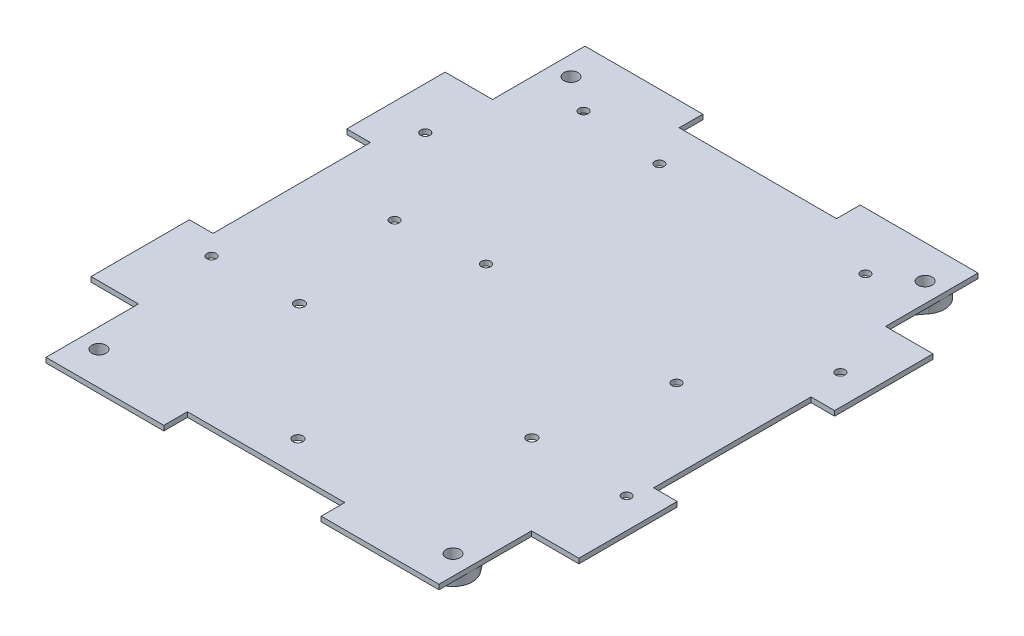
SolidWorks part; units mm, degrees
ref_plane "Front Plane" through (0, 0, 0) normal (0, 0, 1) x (1, 0, 0)
ref_plane "Top Plane" through (0, 0, 0) normal (0, 1, 0) x (1, 0, 0)
ref_plane "Right Plane" through (0, 0, 0) normal (1, 0, 0) x (0, 0, -1)
sketch "Sketch1" plane through (0, 0, 0) normal (0, 1, 0) x (1, 0, 0)
  line L0 (-25.4, 86.995) -> (-63.4314, 86.995)
  line L1 (-88.9, -101.6) -> (88.9, -101.6) construction
  line L2 (101.6, -88.9) -> (101.6, 88.9) construction
  line L3 (88.9, 101.6) -> (-88.9, 101.6) construction
  line L4 (-78.74, -60.96) -> (-63.4314, -60.96)
  line L5 (-63.4314, -60.96) -> (-63.4314, -86.995)
  line L6 (-63.4314, -86.995) -> (-25.4, -86.995)
  line L7 (63.4314, -86.995) -> (63.4314, -60.96)
  line L8 (63.4314, -60.96) -> (78.74, -60.96)
  line L9 (78.74, -60.96) -> (78.74, -25.4)
  line L10 (78.74, 60.96) -> (63.4314, 60.96)
  line L11 (63.4314, 60.96) -> (63.4314, 86.995)
  line L12 (63.4314, 86.995) -> (25.4, 86.995)
  line L13 (-63.4314, 86.995) -> (-63.4314, 60.96)
  line L14 (-63.4314, 60.96) -> (-78.74, 60.96)
  line L15 (-78.74, 60.96) -> (-78.74, 25.4)
  line L16 (-78.74, -25.4) -> (-78.74, -60.96)
  line L17 (-78.74, -25.4) -> (-71.12, -25.4)
  line L19 (-78.74, 25.4) -> (-71.12, 25.4)
  line L20 (-71.12, -25.4) -> (-71.12, 25.4)
  line L22 (-25.4, 86.995) -> (-25.4, 79.375)
  line L23 (-25.4, 79.375) -> (25.4, 79.375)
  line L24 (25.4, 86.995) -> (25.4, 79.375)
  line L25 (78.74, 25.4) -> (71.12, 25.4)
  line L27 (78.74, -25.4) -> (71.12, -25.4)
  line L28 (71.12, 25.4) -> (71.12, -25.4)
  line L30 (25.4, -86.995) -> (25.4, -79.375)
  line L31 (25.4, -79.375) -> (-25.4, -79.375)
  line L32 (-25.4, -86.995) -> (-25.4, -79.375)
  line L33 (78.74, 25.4) -> (78.74, 60.96)
  line L34 (25.4, -86.995) -> (63.4314, -86.995)
  line L35 (-101.6, 88.9) -> (-101.6, -88.9) construction
  line L36 (-78.74, 25.4) -> (-78.74, -25.4)
  line L37 (78.74, 25.4) -> (78.74, -25.4)
  line L38 (-78.74, 0) -> (-91.44, 0)
  line L39 (78.74, 0) -> (91.44, 0)
  line L40 (-91.44, -57.15) -> (-91.44, 57.15)
  line L41 (91.44, -57.15) -> (91.44, 57.15)
  line L42 (-91.44, -57.15) -> (-78.74, -57.15)
  line L43 (-91.44, 57.15) -> (-78.74, 57.15)
  line L44 (91.44, 57.15) -> (78.74, 57.15)
  line L45 (91.44, -57.15) -> (78.74, -57.15)
  line L46 (-78.74, -57.15) -> (-63.4314, -57.15)
  line L47 (-63.4314, -57.15) -> (-63.4314, -60.96)
  line L48 (78.74, -57.15) -> (63.4314, -57.15)
  line L49 (63.4314, -57.15) -> (63.4314, -60.96)
  line L50 (78.74, 57.15) -> (63.4314, 57.15)
  line L51 (63.4314, 57.15) -> (63.4314, 60.96)
  line L52 (-78.74, 57.15) -> (-63.4314, 57.15)
  line L53 (-63.4314, 57.15) -> (-63.4314, 60.96)
  arc A0 (88.9, -101.6) -> (101.6, -88.9) centre (88.9, -88.9) ccw construction
  arc A1 (-101.6, -88.9) -> (-88.9, -101.6) centre (-88.9, -88.9) ccw construction
  arc A2 (101.6, 88.9) -> (88.9, 101.6) centre (88.9, 88.9) ccw construction
  arc A3 (-101.6, 88.9) -> (-88.9, 101.6) centre (-88.9, 88.9) cw construction
  circle A4 centre (-57.15, 76.2) radius 2.286
  circle A5 centre (57.15, 76.2) radius 2.286
  circle A6 centre (57.15, -76.2) radius 2.286
  circle A7 centre (-57.15, -76.2) radius 2.286
  point P3 (0, 101.6)
  point P5 (101.6, 0)
  point P13 (101.6, 101.6)
  point P16 (-101.6, 101.6)
  point P19 (-78.74, 0)
  point P38 (-71.12, 0)
  point P55 (0, -79.375)
  point P56 (0, 79.375)
  point P57 (71.12, 0)
  point P60 (78.74, 0)
  point P66 (-91.44, 0)
  point P69 (91.44, 0)
  dimension "D2" = 12.7
  dimension "D11" = 4.572
  dimension "D8" = 44.45
  dimension "D1" = 203.2
  dimension "D3" = 203.2
  dimension "D4" = 22.86
  dimension "D5" = 15.3086
  dimension "D6" = 35.56
  dimension "D7" = 173.99
  dimension "D9" = 12.7
  dimension "D10" = 114.3
  dimension "D12" = 50.8
  dimension "D13" = 25.4
  dimension "D14" = 44.45
  dimension "D15" = 25.4
  dimension "D18" = 7.62
extrude "Main Body" add sketch "Sketch1" along normal blind 1.5875 contours L53 L52 L15 L19 L20 L17 L16 L46 L47 L5 L6 L32 L31 L30 L34 L7 L49 L48 L9 L27 L28 L25 L33 L50 L51 L11 L12 L24 L23 L22 L0 L13 A7 A6 A5 A4
sketch "Sketch2" plane through (0, 0, 0) normal (0, -1, 0) x (1, 0, 0)
  line L1 (80, 45) -> (-80, 45)
  line L2 (80, 45) -> (80, -45)
  line L3 (80, -45) -> (-80, -45)
  line L4 (-80, 45) -> (-80, -45)
  line L5 (80, 45) -> (-80, -45) construction
  line L6 (80, -45) -> (-80, 45) construction
  line L20 (63.4314, -57.15) -> (78.74, -57.15)
  line L21 (63.4314, 57.15) -> (63.4314, 86.995)
  line L22 (63.4314, 86.995) -> (25.4, 86.995)
  line L23 (25.4, 86.995) -> (25.4, 79.375)
  line L24 (25.4, 79.375) -> (-25.4, 79.375)
  line L25 (-25.4, 79.375) -> (-25.4, 86.995)
  line L26 (-25.4, 86.995) -> (-63.4314, 86.995)
  line L27 (-63.4314, 86.995) -> (-63.4314, 57.15)
  line L28 (63.4314, -57.15) -> (78.74, -57.15)
  line L29 (78.74, -57.15) -> (78.74, -25.4)
  line L30 (78.74, -57.15) -> (78.74, -25.4)
  line L31 (-63.4314, -57.15) -> (-63.4314, -86.995)
  line L32 (-63.4314, -86.995) -> (-25.4, -86.995)
  line L33 (-25.4, -86.995) -> (-25.4, -79.375)
  line L34 (-25.4, -79.375) -> (25.4, -79.375)
  line L35 (25.4, -79.375) -> (25.4, -86.995)
  line L36 (25.4, -86.995) -> (63.4314, -86.995)
  line L37 (63.4314, -86.995) -> (63.4314, -57.15)
  line L38 (78.74, -25.4) -> (71.12, -25.4)
  line L39 (78.74, -25.4) -> (71.12, -25.4)
  line L41 (63.4314, 57.15) -> (63.4314, 86.995)
  line L42 (63.4314, 86.995) -> (25.4, 86.995)
  line L43 (25.4, 86.995) -> (25.4, 79.375)
  line L44 (25.4, 79.375) -> (-25.4, 79.375)
  line L45 (-25.4, 79.375) -> (-25.4, 86.995)
  line L46 (-25.4, 86.995) -> (-63.4314, 86.995)
  line L47 (-63.4314, 86.995) -> (-63.4314, 57.15)
  line L51 (-63.4314, -57.15) -> (-63.4314, -86.995)
  line L52 (-63.4314, -86.995) -> (-25.4, -86.995)
  line L53 (-25.4, -86.995) -> (-25.4, -79.375)
  line L54 (-25.4, -79.375) -> (25.4, -79.375)
  line L55 (25.4, -79.375) -> (25.4, -86.995)
  line L56 (25.4, -86.995) -> (63.4314, -86.995)
  line L57 (63.4314, -86.995) -> (63.4314, -57.15)
  line L74 (71.12, -25.4) -> (71.12, 25.4)
  line L75 (71.12, -25.4) -> (71.12, 25.4)
  line L76 (71.12, 25.4) -> (78.74, 25.4)
  line L77 (71.12, 25.4) -> (78.74, 25.4)
  line L78 (78.74, 25.4) -> (78.74, 57.15)
  line L79 (78.74, 25.4) -> (78.74, 57.15)
  line L80 (78.74, 57.15) -> (63.4314, 57.15)
  line L81 (78.74, 57.15) -> (63.4314, 57.15)
  line L82 (-63.4314, 57.15) -> (-78.74, 57.15)
  line L83 (-63.4314, 57.15) -> (-78.74, 57.15)
  line L84 (-78.74, 57.15) -> (-78.74, 25.4)
  line L85 (-78.74, 57.15) -> (-78.74, 25.4)
  line L86 (-78.74, 25.4) -> (-71.12, 25.4)
  line L87 (-78.74, 25.4) -> (-71.12, 25.4)
  line L88 (-71.12, 25.4) -> (-71.12, -25.4)
  line L89 (-71.12, 25.4) -> (-71.12, -25.4)
  line L90 (-71.12, -25.4) -> (-78.74, -25.4)
  line L91 (-71.12, -25.4) -> (-78.74, -25.4)
  line L92 (-78.74, -25.4) -> (-78.74, -57.15)
  line L93 (-78.74, -25.4) -> (-78.74, -57.15)
  line L94 (-78.74, -57.15) -> (-63.4314, -57.15)
  line L95 (-78.74, -57.15) -> (-63.4314, -57.15)
  circle A0 centre (69, -37) radius 1.5
  circle A1 centre (-65, -37) radius 1.5
  circle A2 centre (-65, 32) radius 1.5
  circle A3 centre (69, 32) radius 1.5
  point P2 (0, 0)
  point P28 (0, 0)
  point P30 (0, 0)
  point P32 (0, 0)
  point P34 (0, 0)
  dimension "D4" = 3
  dimension "D2" = 160
  dimension "D3" = 90
  dimension "D5" = 11
  dimension "D6" = 8
  dimension "D7" = 145
  dimension "D8" = 77
  dimension "D1" = 0
extrude "Cut-Extrude1" cut sketch "Sketch2" against normal up to next contours A0 | A1 | A2 | A3
sketch "Sketch3" plane through (0, 1.5875, 0) normal (0, 1, 0) x (1, 0, 0)
  line L1 (-53, 3.1) -> (53, 3.1)
  line L2 (-53, 3.1) -> (-53, 73.1)
  line L3 (-53, 73.1) -> (53, 73.1)
  line L4 (53, 3.1) -> (53, 73.1)
  line L5 (-53, 3.1) -> (53, 73.1) construction
  line L6 (-53, 73.1) -> (53, 3.1) construction
  line L20 (-63.4314, 57.15) -> (-78.74, 57.15)
  line L21 (-63.4314, 57.15) -> (-78.74, 57.15)
  line L22 (-78.74, 57.15) -> (-78.74, 25.4)
  line L23 (63.4314, 57.15) -> (63.4314, 86.995)
  line L24 (63.4314, 86.995) -> (25.4, 86.995)
  line L25 (25.4, 86.995) -> (25.4, 79.375)
  line L26 (25.4, 79.375) -> (-25.4, 79.375)
  line L27 (-25.4, 79.375) -> (-25.4, 86.995)
  line L28 (-25.4, 86.995) -> (-63.4314, 86.995)
  line L29 (-63.4314, 86.995) -> (-63.4314, 57.15)
  line L30 (-78.74, 57.15) -> (-78.74, 25.4)
  line L31 (-78.74, 25.4) -> (-71.12, 25.4)
  line L32 (-78.74, 25.4) -> (-71.12, 25.4)
  line L33 (-63.4314, -57.15) -> (-63.4314, -86.995)
  line L34 (-63.4314, -86.995) -> (-25.4, -86.995)
  line L35 (-25.4, -86.995) -> (-25.4, -79.375)
  line L36 (-25.4, -79.375) -> (25.4, -79.375)
  line L37 (25.4, -79.375) -> (25.4, -86.995)
  line L38 (25.4, -86.995) -> (63.4314, -86.995)
  line L39 (63.4314, -86.995) -> (63.4314, -57.15)
  line L43 (63.4314, 57.15) -> (63.4314, 86.995)
  line L44 (63.4314, 86.995) -> (25.4, 86.995)
  line L45 (25.4, 86.995) -> (25.4, 79.375)
  line L46 (25.4, 79.375) -> (-25.4, 79.375)
  line L47 (-25.4, 79.375) -> (-25.4, 86.995)
  line L48 (-25.4, 86.995) -> (-63.4314, 86.995)
  line L49 (-63.4314, 86.995) -> (-63.4314, 57.15)
  line L53 (-63.4314, -57.15) -> (-63.4314, -86.995)
  line L54 (-63.4314, -86.995) -> (-25.4, -86.995)
  line L55 (-25.4, -86.995) -> (-25.4, -79.375)
  line L56 (-25.4, -79.375) -> (25.4, -79.375)
  line L57 (25.4, -79.375) -> (25.4, -86.995)
  line L58 (25.4, -86.995) -> (63.4314, -86.995)
  line L59 (63.4314, -86.995) -> (63.4314, -57.15)
  line L74 (-71.12, 25.4) -> (-71.12, -25.4)
  line L75 (-71.12, 25.4) -> (-71.12, -25.4)
  line L76 (-71.12, -25.4) -> (-78.74, -25.4)
  line L77 (-71.12, -25.4) -> (-78.74, -25.4)
  line L78 (-78.74, -25.4) -> (-78.74, -57.15)
  line L79 (-78.74, -25.4) -> (-78.74, -57.15)
  line L80 (-78.74, -57.15) -> (-63.4314, -57.15)
  line L81 (-78.74, -57.15) -> (-63.4314, -57.15)
  line L82 (63.4314, -57.15) -> (78.74, -57.15)
  line L83 (63.4314, -57.15) -> (78.74, -57.15)
  line L84 (78.74, -57.15) -> (78.74, -25.4)
  line L85 (78.74, -57.15) -> (78.74, -25.4)
  line L86 (78.74, -25.4) -> (71.12, -25.4)
  line L87 (78.74, -25.4) -> (71.12, -25.4)
  line L88 (71.12, -25.4) -> (71.12, 25.4)
  line L89 (71.12, -25.4) -> (71.12, 25.4)
  line L90 (71.12, 25.4) -> (78.74, 25.4)
  line L91 (71.12, 25.4) -> (78.74, 25.4)
  line L92 (78.74, 25.4) -> (78.74, 57.15)
  line L93 (78.74, 25.4) -> (78.74, 57.15)
  line L94 (78.74, 57.15) -> (63.4314, 57.15)
  line L95 (78.74, 57.15) -> (63.4314, 57.15)
  circle A0 centre (-18.5, 66.1) radius 1.5
  circle A1 centre (45.5, 68.6) radius 1.5
  circle A2 centre (45.5, 7.6) radius 1.5
  circle A3 centre (-18.5, 10.1) radius 1.5
  circle A4 centre (-45.5, 68.6) radius 1.5
  circle A5 centre (-45.5, 7.6) radius 1.5
  point P2 (0, 38.1)
  point P32 (0, 0)
  point P38 (0, 0)
  point P39 (0, 0)
  dimension "D4" = 3
  dimension "D2" = 106
  dimension "D3" = 70
  dimension "D5" = 38.1
  dimension "D6" = 4.5
  dimension "D7" = 4.5
  dimension "D8" = 7.5
  dimension "D9" = 7
  dimension "D10" = 7
  dimension "D11" = 71.5
  dimension "D12" = 7.5
  dimension "D1" = 0
extrude "Cut-Extrude2" cut sketch "Sketch3" against normal up to next contours A0 | A1 | A2 | A3 | A4 | A5
sketch "Sketch4" plane through (0, 1.5875, 0) normal (0, 1, 0) x (1, 0, 0)
  line L1 (-40.5, -74.1) -> (40.5, -74.1)
  line L2 (-40.5, -74.1) -> (-40.5, -2.1)
  line L3 (-40.5, -2.1) -> (40.5, -2.1)
  line L4 (40.5, -74.1) -> (40.5, -2.1)
  line L5 (-40.5, -74.1) -> (40.5, -2.1) construction
  line L6 (-40.5, -2.1) -> (40.5, -74.1) construction
  line L20 (-63.4314, 57.15) -> (-78.74, 57.15)
  line L21 (-63.4314, 57.15) -> (-78.74, 57.15)
  line L22 (-78.74, 57.15) -> (-78.74, 25.4)
  line L23 (63.4314, 57.15) -> (63.4314, 86.995)
  line L24 (63.4314, 86.995) -> (25.4, 86.995)
  line L25 (25.4, 86.995) -> (25.4, 79.375)
  line L26 (25.4, 79.375) -> (-25.4, 79.375)
  line L27 (-25.4, 79.375) -> (-25.4, 86.995)
  line L28 (-25.4, 86.995) -> (-63.4314, 86.995)
  line L29 (-63.4314, 86.995) -> (-63.4314, 57.15)
  line L30 (-78.74, 57.15) -> (-78.74, 25.4)
  line L31 (-78.74, 25.4) -> (-71.12, 25.4)
  line L32 (-78.74, 25.4) -> (-71.12, 25.4)
  line L33 (-63.4314, -57.15) -> (-63.4314, -86.995)
  line L34 (-63.4314, -86.995) -> (-25.4, -86.995)
  line L35 (-25.4, -86.995) -> (-25.4, -79.375)
  line L36 (-25.4, -79.375) -> (25.4, -79.375)
  line L37 (25.4, -79.375) -> (25.4, -86.995)
  line L38 (25.4, -86.995) -> (63.4314, -86.995)
  line L39 (63.4314, -86.995) -> (63.4314, -57.15)
  line L43 (63.4314, 57.15) -> (63.4314, 86.995)
  line L44 (63.4314, 86.995) -> (25.4, 86.995)
  line L45 (25.4, 86.995) -> (25.4, 79.375)
  line L46 (25.4, 79.375) -> (-25.4, 79.375)
  line L47 (-25.4, 79.375) -> (-25.4, 86.995)
  line L48 (-25.4, 86.995) -> (-63.4314, 86.995)
  line L49 (-63.4314, 86.995) -> (-63.4314, 57.15)
  line L53 (-63.4314, -57.15) -> (-63.4314, -86.995)
  line L54 (-63.4314, -86.995) -> (-25.4, -86.995)
  line L55 (-25.4, -86.995) -> (-25.4, -79.375)
  line L56 (-25.4, -79.375) -> (25.4, -79.375)
  line L57 (25.4, -79.375) -> (25.4, -86.995)
  line L58 (25.4, -86.995) -> (63.4314, -86.995)
  line L59 (63.4314, -86.995) -> (63.4314, -57.15)
  line L74 (-71.12, 25.4) -> (-71.12, -25.4)
  line L75 (-71.12, 25.4) -> (-71.12, -25.4)
  line L76 (-71.12, -25.4) -> (-78.74, -25.4)
  line L77 (-71.12, -25.4) -> (-78.74, -25.4)
  line L78 (-78.74, -25.4) -> (-78.74, -57.15)
  line L79 (-78.74, -25.4) -> (-78.74, -57.15)
  line L80 (-78.74, -57.15) -> (-63.4314, -57.15)
  line L81 (-78.74, -57.15) -> (-63.4314, -57.15)
  line L82 (63.4314, -57.15) -> (78.74, -57.15)
  line L83 (63.4314, -57.15) -> (78.74, -57.15)
  line L84 (78.74, -57.15) -> (78.74, -25.4)
  line L85 (78.74, -57.15) -> (78.74, -25.4)
  line L86 (78.74, -25.4) -> (71.12, -25.4)
  line L87 (78.74, -25.4) -> (71.12, -25.4)
  line L88 (71.12, -25.4) -> (71.12, 25.4)
  line L89 (71.12, -25.4) -> (71.12, 25.4)
  line L90 (71.12, 25.4) -> (78.74, 25.4)
  line L91 (71.12, 25.4) -> (78.74, 25.4)
  line L92 (78.74, 25.4) -> (78.74, 57.15)
  line L93 (78.74, 25.4) -> (78.74, 57.15)
  line L94 (78.74, 57.15) -> (63.4314, 57.15)
  line L95 (78.74, 57.15) -> (63.4314, 57.15)
  circle A0 centre (-37.5, -31.1) radius 1.625
  circle A1 centre (37.5, -31.1) radius 1.625
  circle A2 centre (0, -69.1) radius 1.625
  point P2 (0, -38.1)
  point P20 (0, 0)
  dimension "D5" = 3.25
  dimension "D2" = 81
  dimension "D3" = 72
  dimension "D4" = 38.1
  dimension "D6" = 43
  dimension "D7" = 3
  dimension "D8" = 3
  dimension "D9" = 5
  dimension "D1" = 0
extrude "Cut-Extrude3" cut sketch "Sketch4" against normal up to next contours A0 | A1 | A2
sketch "Sketch5" plane through (0, 0, 0) normal (0, -1, 0) x (1, 0, 0)
  line L0 (0, -10.469) -> (52.1249, -79.9689)
  line L5 (62.1751, -72.4311) -> (52.1249, -79.9689)
  line L6 (62.1751, -72.4311) -> (8.2383, -0.5153)
  line L7 (-62.1751, -72.4311) -> (-8.9334, -1.4422)
  line L8 (-52.1249, -79.9689) -> (0, -10.469)
  line L9 (-62.1751, -72.4311) -> (-52.1249, -79.9689)
  line L10 (8.2383, -0.5153) -> (7.8518, 0)
  line L11 (-52.1249, 79.9689) -> (-62.1751, 72.4311)
  line L12 (-62.1751, 72.4311) -> (-7.8518, 0)
  line L13 (52.1249, 79.9689) -> (62.1751, 72.4311)
  line L14 (7.8518, 0) -> (62.1751, 72.4311)
  line L15 (52.1249, 79.9689) -> (0, 10.469)
  line L16 (0, 10.469) -> (-52.1249, 79.9689)
  line L17 (-7.8518, 0) -> (-8.9334, -1.4422)
  line L20 (63.4314, -57.15) -> (78.74, -57.15)
  line L21 (63.4314, 57.15) -> (63.4314, 86.995)
  line L22 (63.4314, 86.995) -> (25.4, 86.995)
  line L23 (25.4, 86.995) -> (25.4, 79.375)
  line L24 (25.4, 79.375) -> (-25.4, 79.375)
  line L25 (-25.4, 79.375) -> (-25.4, 86.995)
  line L26 (-25.4, 86.995) -> (-63.4314, 86.995)
  line L27 (-63.4314, 86.995) -> (-63.4314, 57.15)
  line L28 (63.4314, -57.15) -> (78.74, -57.15)
  line L29 (78.74, -57.15) -> (78.74, -25.4)
  line L30 (78.74, -57.15) -> (78.74, -25.4)
  line L31 (-63.4314, -57.15) -> (-63.4314, -86.995)
  line L32 (-63.4314, -86.995) -> (-25.4, -86.995)
  line L33 (-25.4, -86.995) -> (-25.4, -79.375)
  line L34 (-25.4, -79.375) -> (25.4, -79.375)
  line L35 (25.4, -79.375) -> (25.4, -86.995)
  line L36 (25.4, -86.995) -> (63.4314, -86.995)
  line L37 (63.4314, -86.995) -> (63.4314, -57.15)
  line L38 (78.74, -25.4) -> (71.12, -25.4)
  line L39 (78.74, -25.4) -> (71.12, -25.4)
  line L41 (63.4314, 57.15) -> (63.4314, 86.995)
  line L42 (63.4314, 86.995) -> (25.4, 86.995)
  line L43 (25.4, 86.995) -> (25.4, 79.375)
  line L44 (25.4, 79.375) -> (-25.4, 79.375)
  line L45 (-25.4, 79.375) -> (-25.4, 86.995)
  line L46 (-25.4, 86.995) -> (-63.4314, 86.995)
  line L47 (-63.4314, 86.995) -> (-63.4314, 57.15)
  line L51 (-63.4314, -57.15) -> (-63.4314, -86.995)
  line L52 (-63.4314, -86.995) -> (-25.4, -86.995)
  line L53 (-25.4, -86.995) -> (-25.4, -79.375)
  line L54 (-25.4, -79.375) -> (25.4, -79.375)
  line L55 (25.4, -79.375) -> (25.4, -86.995)
  line L56 (25.4, -86.995) -> (63.4314, -86.995)
  line L57 (63.4314, -86.995) -> (63.4314, -57.15)
  line L86 (71.12, -25.4) -> (71.12, 25.4)
  line L87 (71.12, -25.4) -> (71.12, 25.4)
  line L88 (71.12, 25.4) -> (78.74, 25.4)
  line L89 (71.12, 25.4) -> (78.74, 25.4)
  line L90 (78.74, 25.4) -> (78.74, 57.15)
  line L91 (78.74, 25.4) -> (78.74, 57.15)
  line L92 (78.74, 57.15) -> (63.4314, 57.15)
  line L93 (78.74, 57.15) -> (63.4314, 57.15)
  line L94 (-63.4314, 57.15) -> (-78.74, 57.15)
  line L95 (-63.4314, 57.15) -> (-78.74, 57.15)
  line L96 (-78.74, 57.15) -> (-78.74, 25.4)
  line L97 (-78.74, 57.15) -> (-78.74, 25.4)
  line L98 (-78.74, 25.4) -> (-71.12, 25.4)
  line L99 (-78.74, 25.4) -> (-71.12, 25.4)
  line L100 (-71.12, 25.4) -> (-71.12, -25.4)
  line L101 (-71.12, 25.4) -> (-71.12, -25.4)
  line L102 (-71.12, -25.4) -> (-78.74, -25.4)
  line L103 (-71.12, -25.4) -> (-78.74, -25.4)
  line L104 (-78.74, -25.4) -> (-78.74, -57.15)
  line L105 (-78.74, -25.4) -> (-78.74, -57.15)
  line L106 (-78.74, -57.15) -> (-63.4314, -57.15)
  line L107 (-78.74, -57.15) -> (-63.4314, -57.15)
  circle A0 centre (57.15, -76.2) radius 6.2814
  circle A1 centre (-57.15, -76.2) radius 6.2814
  circle A2 centre (57.15, 76.2) radius 6.2814
  circle A3 centre (-57.15, 76.2) radius 6.2814
  circle A4 centre (57.15, -76.2) radius 2.286 construction
  circle A5 centre (57.15, -76.2) radius 2.286
  circle A6 centre (57.15, 76.2) radius 2.286 construction
  circle A7 centre (-57.15, 76.2) radius 2.286 construction
  circle A8 centre (-57.15, -76.2) radius 2.286 construction
  circle A9 centre (57.15, 76.2) radius 2.286
  circle A10 centre (-57.15, 76.2) radius 2.286
  circle A11 centre (-57.15, -76.2) radius 2.286
  point P50 (57.15, -76.2)
  point P52 (-57.15, -76.2)
  point P56 (-57.15, 76.2)
  point P57 (57.15, 76.2)
  circle M24 centre (45.5, -68.6) radius 1.5
  circle M27 centre (-45.5, -68.6) radius 1.5
  circle M54 centre (-57.15, 76.2) radius 2.286
  circle M55 centre (57.15, 76.2) radius 2.286
  circle M56 centre (57.15, -76.2) radius 2.286
  circle M57 centre (-57.15, -76.2) radius 2.286
  dimension "D2" = 12.7
  dimension "D3" = 90
  dimension "D4" = 90
  dimension "D5" = 90
  dimension "D1" = 0
extrude "Boss-Extrude1" add sketch "Sketch5" along normal blind 3.175 contours A3 L12 L17 L7 A1 L8 L0 A0 L6 L10 L14 A2 L15 L16 M27 M24 | A0 L5 M56 | L5 A0 M56 | L9 A1 M57 | L9 A1 M57 | L11 A3 M54 | L11 A3 M54 | L13 A2 M55 | L13 A2 M55
sketch "Sketch14" plane through (0, -3.175, 0) normal (0, -1, 0) x (1, 0, 0)
  line L8 (-62.1751, 72.4311) -> (-7.8518, 0)
  line L9 (-7.8518, 0) -> (-62.1751, -72.4311)
  line L10 (-52.1249, -79.9689) -> (0, -10.469)
  line L11 (0, -10.469) -> (52.1249, -79.9689)
  line L12 (62.1751, -72.4311) -> (7.8518, 0)
  line L13 (7.8518, 0) -> (62.1751, 72.4311)
  line L14 (52.1249, 79.9689) -> (0, 10.469)
  line L15 (0, 10.469) -> (-52.1249, 79.9689)
  line L16 (-62.1751, 72.4311) -> (-7.8518, 0)
  line L17 (-7.8518, 0) -> (-62.1751, -72.4311)
  line L18 (-52.1249, -79.9689) -> (0, -10.469)
  line L19 (0, -10.469) -> (52.1249, -79.9689)
  line L20 (62.1751, -72.4311) -> (7.8518, 0)
  line L21 (7.8518, 0) -> (62.1751, 72.4311)
  line L22 (52.1249, 79.9689) -> (0, 10.469)
  line L23 (0, 10.469) -> (-52.1249, 79.9689)
  circle A0 centre (45.5, -68.6) radius 1.5 construction
  circle A1 centre (-45.5, -68.6) radius 1.5 construction
  circle A2 centre (45.5, -68.6) radius 1.5
  circle A3 centre (-45.5, -68.6) radius 1.5
  arc A4 (-52.1249, 79.9689) -> (-62.1751, 72.4311) centre (-57.15, 76.2) ccw
  arc A5 (-62.1751, -72.4311) -> (-52.1249, -79.9689) centre (-57.15, -76.2) ccw
  arc A6 (52.1249, -79.9689) -> (62.1751, -72.4311) centre (57.15, -76.2) ccw
  arc A7 (62.1751, 72.4311) -> (52.1249, 79.9689) centre (57.15, 76.2) ccw
  arc A8 (-52.1249, 79.9689) -> (-62.1751, 72.4311) centre (-57.15, 76.2) ccw
  arc A9 (-62.1751, -72.4311) -> (-52.1249, -79.9689) centre (-57.15, -76.2) ccw
  arc A10 (52.1249, -79.9689) -> (62.1751, -72.4311) centre (57.15, -76.2) ccw
  arc A11 (62.1751, 72.4311) -> (52.1249, 79.9689) centre (57.15, 76.2) ccw
  circle A12 centre (45.5, -68.6) radius 4.7625
  circle A13 centre (-45.5, -68.6) radius 4.7625
  circle M33 centre (-45.5, -68.6) radius 1.5
  circle M34 centre (45.5, -68.6) radius 1.5
  dimension "D2" = 9.525
  dimension "D1" = 0
extrude "Cut-Extrude7" cut sketch "Sketch14" against normal up to surface (3.175 mm away) contours L19 A12 M34 | L18 A13 M33 up to face at (-18.5, 0, -64.6)
fillet "Fillet2" radius 1.5875 4 edges at (-41.5751, -1.5875, -65.9025) (-46.9906, -1.5875, -73.1232) (46.9906, -1.5875, -73.1232) (41.5751, -1.5875, -65.9025)
